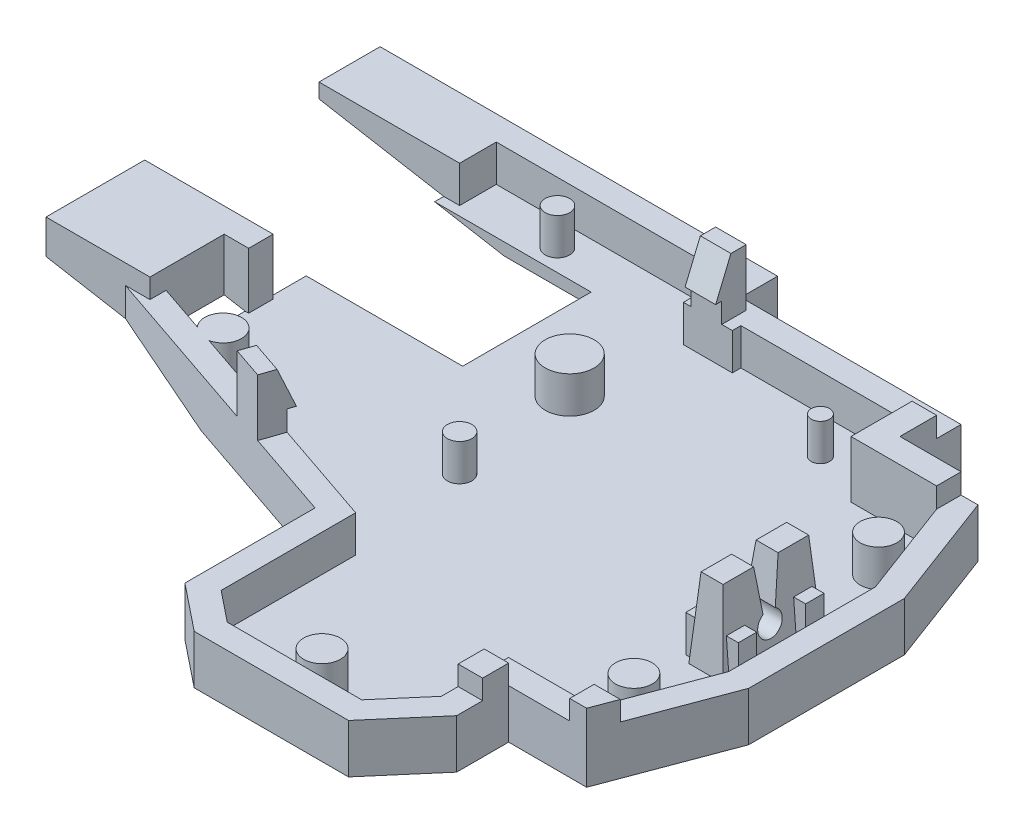
SolidWorks part; units mm, degrees
ref_plane "Front Plane" through (0, 0, 0) normal (0, 0, 1) x (1, 0, 0)
ref_plane "Top Plane" through (0, 0, 0) normal (0, 1, 0) x (1, 0, 0)
ref_plane "Right Plane" through (0, 0, 0) normal (1, 0, 0) x (0, 0, -1)
sketch "Sketch13" plane through (0, 0, 0) normal (0, 1, 0) x (1, 0, 0)
  line L1 (0, 0) -> (50, 0)
  line L2 (0, 0) -> (0, -45)
  line L3 (0, -45) -> (50, -45)
  line L4 (50, 0) -> (50, -45)
  dimension "D1" = 50
extrude "Boss-Extrude4" add sketch "Sketch13" along normal blind 1.6
sketch "Sketch14" plane through (0, 1.6, 0) normal (0, 1, 0) x (1, 0, 0)
  line L1 (50, 0) -> (40, 0)
  line L2 (50, 0) -> (50, -8)
  line L3 (50, -8) -> (40, -8)
  line L4 (40, 0) -> (40, -8)
extrude "Cut-Extrude6" cut sketch "Sketch14" against normal through all
sketch "Sketch15" plane through (0, 1.6, 0) normal (0, 1, 0) x (1, 0, 0)
  line L1 (40, 0) -> (22, 0)
  line L2 (40, 0) -> (40, -3)
  line L3 (40, -3) -> (22, -3)
  line L4 (22, 0) -> (22, -3)
extrude "Cut-Extrude7" cut sketch "Sketch15" against normal through all
sketch "Sketch16" plane through (0, 1.6, 0) normal (0, 1, 0) x (1, 0, 0)
  line L1 (22, -3) -> (26, -3)
  line L2 (22, -3) -> (22, -3.7)
  line L3 (22, -3.7) -> (26, -3.7)
  line L4 (26, -3) -> (26, -3.7)
  dimension "D1" = 0.7
  dimension "D2" = 4
extrude "Cut-Extrude8" cut sketch "Sketch16" against normal through all
sketch "Sketch17" plane through (0, 1.6, 0) normal (0, 1, 0) x (1, 0, 0)
  line L3 (40, -8) -> (50, -8) construction
  line L4 (47, -8) -> (50, -16)
  line L6 (50, -45) -> (50, -8) construction
  line L7 (50, -16) -> (65.8811, -16)
  line L8 (65.8811, -16) -> (65.8811, 17.9573)
  line L9 (65.8811, 17.9573) -> (47, 17.9573)
  line L10 (47, 17.9573) -> (47, -8)
extrude "Cut-Extrude9" cut sketch "Sketch17" against normal through all
sketch "Sketch18" plane through (0, 1.6, 0) normal (0, 1, 0) x (1, 0, 0)
  line L0 (40, -8) -> (40, -36) construction
  line L2 (40, -36) -> (61.1096, -36)
  line L3 (40, -36) -> (40, -58.8405)
  line L4 (40, -58.8405) -> (61.1096, -58.8405)
  line L5 (61.1096, -36) -> (61.1096, -58.8405)
extrude "Cut-Extrude10" cut sketch "Sketch18" against normal through all
sketch "Sketch21" plane through (0, 1.6, 0) normal (0, 1, 0) x (1, 0, 0)
  line L0 (50, -16) -> (27.9365, -16) construction
  line L1 (47, -36) -> (47, -28) construction
  line L2 (50, -36) -> (40, -36) construction
  line L3 (50, -28) -> (47, -36)
  line L4 (50, -36) -> (50, -16) construction
  line L5 (47, -36) -> (47, -49.2976)
  line L6 (47, -49.2976) -> (75.1968, -49.2976)
  line L7 (75.1968, -49.2976) -> (75.1968, -28)
  line L8 (75.1968, -28) -> (50, -28)
extrude "Cut-Extrude11" cut sketch "Sketch21" against normal through all
sketch "Sketch22" plane through (0, 1.6, 0) normal (0, 1, 0) x (1, 0, 0)
  line L0 (0, 0) -> (0, -19.3362) construction
  line L1 (0, 0) -> (0, -45) construction
  line L4 (0, -19.3362) -> (2, -19.3362)
  line L5 (0, -19.3362) -> (0, -22.3362)
  line L6 (0, -22.3362) -> (2, -22.3362)
  line L7 (2, -19.3362) -> (2, -22.3362)
  dimension "D1" = 2
  dimension "D2" = 3
extrude "Cut-Extrude12" cut sketch "Sketch22" against normal through all
sketch "Sketch23" plane through (0, 1.6, 0) normal (0, 1, 0) x (1, 0, 0)
  line L0 (40, -45) -> (23.5, -45) construction
  line L1 (0, -45) -> (40, -45) construction
  line L2 (23.5, -45) -> (23.5, -32)
  line L3 (0, -22.3362) -> (0, -26.3362) construction
  line L4 (0, -22.3362) -> (0, -45) construction
  line L5 (23.5, -32) -> (0, -26.3362)
  line L6 (0, -26.3362) -> (-30.2262, -26.3362)
  line L7 (-30.2262, -26.3362) -> (-30.2262, -63.1883)
  line L8 (-30.2262, -63.1883) -> (23.5, -63.1883)
  line L9 (23.5, -63.1883) -> (23.5, -45)
extrude "Cut-Extrude13" cut sketch "Sketch23" against normal through all
sketch "Sketch24" plane through (0, 1.6, 0) normal (0, 1, 0) x (1, 0, 0)
  line L0 (23.5, -43) -> (7.4911, -43)
  line L1 (23.5, -45) -> (40, -45) construction
  line L2 (7.4911, -43) -> (7.4911, -69.5502)
  line L3 (40, -36) -> (40, -45) construction
  line L4 (37, -45) -> (40, -41.5)
  line L5 (23.5, -45) -> (23.5, -32) construction
  line L6 (26, -45) -> (23.5, -43)
  line L7 (7.4911, -69.5502) -> (44.754, -69.5502)
  line L8 (44.754, -69.5502) -> (44.754, -41.5)
  line L9 (44.754, -41.5) -> (40, -41.5)
  line L10 (37, -45) -> (26, -45)
extrude "Cut-Extrude14" cut sketch "Sketch24" against normal through all
sketch "Sketch25" plane through (0, 1.6, 0) normal (0, 1, 0) x (1, 0, 0)
  line L0 (50, -22) -> (47.6007, -22.0598) construction
  line L1 (50, -28) -> (50, -16) construction
  line L2 (47.6007, -22.0598) -> (47.6007, -18.0598) construction
  line L4 (47.6007, -18.0598) -> (44.8007, -18.0598)
  line L5 (47.6007, -18.0598) -> (47.6007, -26.0598)
  line L6 (47.6007, -26.0598) -> (44.8007, -26.0598)
  line L7 (44.8007, -18.0598) -> (44.8007, -26.0598)
  dimension "D1" = 2.8
  dimension "D2" = 8
extrude "Cut-Extrude15" cut sketch "Sketch25" against normal through all
sketch "Sketch28" plane through (0, 0, 0) normal (0, -1, 0) x (1, 0, 0)
  line L44 (42, 38) -> (42, 42.2398)
  line L45 (42, 42.2398) -> (37.9199, 47)
  line L46 (37.9199, 47) -> (25.2984, 47)
  line L47 (25.2984, 47) -> (21.5, 43.9612)
  line L48 (21.5, 43.9612) -> (21.5, 33.5752)
  line L49 (21.5, 33.5752) -> (-2, 27.9115)
  line L50 (-2, 27.9115) -> (-2, -2)
  line L51 (-2, -2) -> (24, -2)
  line L52 (24, -2) -> (24, 1)
  line L53 (24, 1) -> (42, 1)
  line L54 (42, 1) -> (42, 6)
  line L55 (42, 6) -> (48.386, 6)
  line L56 (48.386, 6) -> (52, 15.6373)
  line L57 (52, 15.6373) -> (52, 28.3627)
  line L58 (52, 28.3627) -> (48.386, 38)
  line L59 (48.386, 38) -> (42, 38)
  line L60 (42, 38) -> (42, 42.2398)
  line L61 (42, 42.2398) -> (37.9199, 47)
  line L62 (37.9199, 47) -> (25.2984, 47)
  line L63 (25.2984, 47) -> (21.5, 43.9612)
  line L64 (21.5, 43.9612) -> (21.5, 33.5752)
  line L65 (21.5, 33.5752) -> (-2, 27.9115)
  line L66 (-2, 27.9115) -> (-2, -2)
  line L67 (-2, -2) -> (24, -2)
  line L68 (24, -2) -> (24, 1)
  line L69 (24, 1) -> (42, 1)
  line L70 (42, 1) -> (42, 6)
  line L71 (42, 6) -> (48.386, 6)
  line L72 (48.386, 6) -> (52, 15.6373)
  line L73 (52, 15.6373) -> (52, 28.3627)
  line L74 (52, 28.3627) -> (48.386, 38)
  line L75 (48.386, 38) -> (42, 38)
  dimension "D1" = 2
extrude "Boss-Extrude6" add sketch "Sketch28" along normal blind 6
sketch "Sketch30" plane through (0, 0, 0) normal (0, 1, 0) x (1, 0, 0)
  line L8 (44.8007, -18.0598) -> (44.8007, -26.0598)
  line L9 (44.8007, -26.0598) -> (47.6007, -26.0598)
  line L10 (47.6007, -26.0598) -> (47.6007, -18.0598)
  line L11 (47.6007, -18.0598) -> (44.8007, -18.0598)
  line L12 (44.8007, -18.0598) -> (44.8007, -26.0598)
  line L13 (44.8007, -26.0598) -> (47.6007, -26.0598)
  line L14 (47.6007, -26.0598) -> (47.6007, -18.0598)
  line L15 (47.6007, -18.0598) -> (44.8007, -18.0598)
  dimension "D1" = 0
extrude "Boss-Extrude7" add sketch "Sketch30" along normal blind 3.5
sketch "Sketch31" plane through (0, 1.6, 0) normal (0, 1, 0) x (1, 0, 0)
  line L44 (37, -45) -> (40, -41.5)
  line L45 (40, -41.5) -> (40, -36)
  line L46 (40, -36) -> (47, -36)
  line L47 (47, -36) -> (50, -28)
  line L48 (50, -28) -> (50, -16)
  line L49 (50, -16) -> (47, -8)
  line L50 (47, -8) -> (40, -8)
  line L51 (40, -8) -> (40, -3)
  line L52 (40, -3) -> (26, -3)
  line L53 (26, -3) -> (26, -3.7)
  line L54 (26, -3.7) -> (22, -3.7)
  line L55 (22, -3.7) -> (22, 0)
  line L56 (22, 0) -> (0, 0)
  line L57 (0, 0) -> (0, -19.3362)
  line L58 (0, -19.3362) -> (2, -19.3362)
  line L59 (2, -19.3362) -> (2, -22.3362)
  line L60 (2, -22.3362) -> (0, -22.3362)
  line L61 (0, -22.3362) -> (0, -26.3362)
  line L62 (0, -26.3362) -> (23.5, -32)
  line L63 (23.5, -32) -> (23.5, -43)
  line L64 (23.5, -43) -> (26, -45)
  line L65 (26, -45) -> (37, -45)
  line L66 (37, -45) -> (40, -41.5)
  line L67 (40, -41.5) -> (40, -36)
  line L68 (40, -36) -> (47, -36)
  line L69 (47, -36) -> (50, -28)
  line L70 (50, -28) -> (50, -16)
  line L71 (50, -16) -> (47, -8)
  line L72 (47, -8) -> (40, -8)
  line L73 (40, -8) -> (40, -3)
  line L74 (40, -3) -> (26, -3)
  line L75 (26, -3) -> (26, -3.7)
  line L76 (26, -3.7) -> (22, -3.7)
  line L77 (22, -3.7) -> (22, 0)
  line L78 (22, 0) -> (0, 0)
  line L79 (0, 0) -> (0, -19.3362)
  line L80 (0, -19.3362) -> (2, -19.3362)
  line L81 (2, -19.3362) -> (2, -22.3362)
  line L82 (2, -22.3362) -> (0, -22.3362)
  line L83 (0, -22.3362) -> (0, -26.3362)
  line L84 (0, -26.3362) -> (23.5, -32)
  line L85 (23.5, -32) -> (23.5, -43)
  line L86 (23.5, -43) -> (26, -45)
  line L87 (26, -45) -> (37, -45)
  dimension "D1" = 0
extrude "Cut-Extrude16" cut sketch "Sketch31" against normal blind 4.6
sketch "Sketch32" plane through (0, 1.6, 0) normal (0, -1, 0) x (1, 0, 0)
  line L8 (47.6007, 18.0598) -> (47.6007, 26.0598)
  line L9 (47.6007, 26.0598) -> (44.8007, 26.0598)
  line L10 (44.8007, 26.0598) -> (44.8007, 18.0598)
  line L11 (44.8007, 18.0598) -> (47.6007, 18.0598)
  line L12 (47.6007, 18.0598) -> (47.6007, 26.0598)
  line L13 (47.6007, 26.0598) -> (44.8007, 26.0598)
  line L14 (44.8007, 26.0598) -> (44.8007, 18.0598)
  line L15 (44.8007, 18.0598) -> (47.6007, 18.0598)
  dimension "D1" = 0
extrude "Boss-Extrude8" add sketch "Sketch32" along normal blind 4.6
sketch "Sketch35" plane through (47.6007, 0, 0) normal (1, 0, 0) x (0, 0, -1)
  line L0 (-22.0598, 3.5) -> (-22.0598, 0) construction
  line L1 (-26.0598, 3.5) -> (-18.0598, 3.5) construction
  line L2 (-22.0598, 3.5) -> (-21.0598, 3.5) construction
  line L3 (-22.0598, 3.5) -> (-23.0598, 3.5) construction
  line L4 (-22.0598, 0) -> (-21.5598, 0)
  line L5 (-21.5598, 0) -> (-21.0598, 3.5)
  line L6 (-22.0598, 0) -> (-22.5598, 0)
  line L7 (-22.5598, 0) -> (-23.0598, 3.5)
  line L8 (-23.0598, 3.5) -> (-23.2577, 4.8851)
  line L9 (-21.0598, 3.5) -> (-21.2977, 5.1651)
  line L10 (-21.2977, 5.1651) -> (-23.2577, 4.8851)
extrude "Cut-Extrude18" cut sketch "Sketch35" against normal blind 4.6
sketch "Sketch37" plane through (47.6007, 0, 0) normal (1, 0, 0) x (0, 0, -1)
  line L0 (-22.0598, 0) -> (-22.0598, -3.4808) construction
  line L1 (-22.5598, 0) -> (-21.5598, 0) construction
  line L2 (-21.5598, 0) -> (-22.0598, -0.866) construction
  circle A0 centre (-22.0598, -0.866) radius 1
extrude "Cut-Extrude19" cut sketch "Sketch37" against normal blind 4.6
sketch "Sketch39" plane through (44.8007, 0, 0) normal (-1, 0, 0) x (0, 0, 1)
  line L0 (26.0598, 3.5) -> (25.5598, 3.5) construction
  line L1 (23.0598, 3.5) -> (26.0598, 3.5) construction
  line L2 (25.5598, 3.5) -> (26.0598, -3)
  line L3 (26.0598, -3) -> (27.9064, -2.858)
  line L4 (27.9064, -2.858) -> (27.4064, 3.642)
  line L5 (27.4064, 3.642) -> (25.5598, 3.5)
  line L6 (18.0598, 3.5) -> (18.5598, 3.5) construction
  line L7 (18.0598, 3.5) -> (21.0598, 3.5) construction
  line L8 (18.5598, 3.5) -> (18.0598, -3)
  line L9 (18.0598, -3) -> (15.9573, -2.8383)
  line L10 (15.9573, -2.8383) -> (16.4557, 3.642)
  line L11 (16.4557, 3.642) -> (18.5598, 3.5)
extrude "Cut-Extrude20" cut sketch "Sketch39" against normal blind 4.6
sketch "Sketch41" plane through (0, 0, 0) normal (0, 0, 1) x (1, 0, 0)
  line L0 (44.8007, 3.5) -> (45.3007, 3.5) construction
  line L1 (44.8007, 3.5) -> (47.6007, 3.5) construction
  line L2 (47.6007, 3.5) -> (47.1007, 3.5) construction
  line L3 (45.3007, 3.5) -> (44.8007, -3)
  line L4 (44.8007, -3) -> (43.415, -2.8934)
  line L5 (43.415, -2.8934) -> (43.9406, 3.9398)
  line L6 (43.9406, 3.9398) -> (45.3007, 3.5)
  line L7 (47.1007, 3.5) -> (47.6007, -3)
  line L8 (47.6007, -3) -> (49.659, -2.8417)
  line L9 (49.659, -2.8417) -> (49.1373, 3.9398)
  line L10 (49.1373, 3.9398) -> (47.1007, 3.5)
extrude "Cut-Extrude21" cut sketch "Sketch41" along normal up to vertex
sketch "Sketch43" plane through (0, 0, 0) normal (0, 1, 0) x (1, 0, 0)
  line L0 (47, -8) -> (50, -16)
  line L1 (50, -16) -> (51.1704, -13.4251)
  line L2 (49.4404, -8.8117) -> (52, -15.6373) construction
  line L3 (46.2007, -6) -> (51.8278, -6) construction
  line L4 (45.0315, -6) -> (47.37, -6) construction
  line L5 (50.6159, -11.9464) -> (47.8466, -4.5615) construction
  line L6 (51.1704, -13.4251) -> (48.386, -6)
  line L7 (48.386, -6) -> (42.8188, -6)
  line L8 (42, -6) -> (43.6375, -6) construction
  line L9 (42.8188, -6) -> (42.8188, -8)
  line L10 (40, -8) -> (43.6375, -8) construction
  line L11 (42.8188, -8) -> (47, -8)
extrude "Boss-Extrude9" add sketch "Sketch43" against normal blind 4.6
sketch "Sketch44" plane through (0, -3, 0) normal (0, 1, 0) x (1, 0, 0)
  line L0 (47.6007, -18.0598) -> (47.6007, -18.5598) construction
  line L1 (47.6007, -18.0598) -> (47.6007, -26.0598) construction
  line L2 (47.6007, -18.5598) -> (48.3507, -18.5598) construction
  line L3 (44.8007, -18.5598) -> (44.0507, -18.5598) construction
  line L4 (44.8007, -26.0598) -> (44.8007, -18.0598) construction
  line L5 (47.6007, -26.0598) -> (47.6007, -25.5598) construction
  line L6 (48.3507, -25.5598) -> (44.0507, -25.5598) construction
  line L7 (48.3507, -18.5598) -> (48.3507, -20.0598)
  line L8 (48.3507, -25.5598) -> (48.3507, -24.0598)
  line L9 (48.3507, -24.0598) -> (44.0507, -24.0598)
  line L10 (44.0507, -24.0598) -> (44.0507, -25.5598)
  line L11 (44.0507, -25.5598) -> (48.3507, -25.5598)
  line L12 (48.3507, -20.0598) -> (44.0507, -20.0598)
  line L13 (44.0507, -20.0598) -> (44.0507, -18.5598)
  line L14 (44.0507, -18.5598) -> (48.3507, -18.5598)
extrude "Boss-Extrude11" add sketch "Sketch44" along normal blind 3
sketch "Sketch45" plane through (0, -3, 0) normal (0, 1, 0) x (1, 0, 0)
  line L0 (50, -22) -> (44, -22) construction
  line L1 (50, -28) -> (50, -16) construction
  line L2 (44, -22) -> (44, -32) construction
  line L3 (44, -32) -> (46.25, -32) construction
  line L4 (44, -22) -> (44, -12) construction
  line L5 (22, -3.7) -> (22, -22) construction
  line L6 (22, -22) -> (22, -21) construction
  line L7 (40, -36) -> (23.5, -36) construction
  line L8 (23.5, -32) -> (23.5, -43) construction
  line L9 (31.75, -45) -> (31.75, -43) construction
  line L10 (26, -45) -> (37, -45) construction
  line L11 (40, -3) -> (40, -6) construction
  line L12 (40, -8) -> (40, -3) construction
  line L13 (40, -6) -> (35.5, -6) construction
  line L14 (22, 0) -> (22, -2) construction
  line L15 (22, 0) -> (0, 0) construction
  line L16 (22, -3.7) -> (22, 0) construction
  line L17 (22, -2) -> (10, -2) construction
  line L18 (0, -24.3362) -> (5, -24.3362) construction
  line L19 (0, -22.3362) -> (0, -26.3362) construction
  circle A0 centre (46.25, -12) radius 1.5
  circle A1 centre (46.25, -32) radius 1.5
  circle A2 centre (22, -22) radius 1
  circle A3 centre (21, -12) radius 1.9996
  circle A4 centre (31.75, -43) radius 1.5033
  circle A5 centre (35.5, -6) radius 0.75
  circle A6 centre (10, -2) radius 1
  circle A7 centre (5, -24.3362) radius 1.5
extrude "Boss-Extrude12" add sketch "Sketch45" along normal blind 3
sketch "Sketch46" plane through (0, 0, 0) normal (0, 1, 0) x (1, 0, 0)
  line L0 (14.1373, -29.7435) -> (16.5677, -30.3292)
  line L1 (16.5677, -30.3292) -> (16.0991, -32.2736)
  line L2 (21.5, -33.5752) -> (-2, -27.9115) construction
  line L3 (16.0991, -32.2736) -> (13.6687, -31.6878)
  line L4 (13.6687, -31.6878) -> (14.1373, -29.7435)
  line L5 (24, -3.7) -> (25.1336, -3.7) construction
  line L6 (22, -3.7) -> (26, -3.7) construction
  line L7 (25.1336, -3.7) -> (22.6336, -3.7)
  line L8 (22.6336, -3.7) -> (22.6336, -1.7)
  line L9 (22.6336, -1.7) -> (25.1336, -1.7)
  line L10 (25.1336, -1.7) -> (25.1336, -3.7)
  line L11 (2, -20.8362) -> (2, -19.9327) construction
  line L12 (2, -22.3362) -> (2, -19.3362) construction
  line L13 (2, -19.9327) -> (2, -21.9327)
  line L14 (2, -21.9327) -> (0, -21.9327)
  line L15 (0, -21.9327) -> (0, -19.9327)
  line L16 (0, -19.9327) -> (2, -19.9327)
  line L17 (23.5, -32) -> (0, -26.3362) construction
  line L18 (16.5677, -30.3292) -> (14.1373, -29.7435) construction
  line L19 (47, -36) -> (48.8727, -36.7022)
  line L20 (52, -28.3627) -> (48.386, -38) construction
  line L21 (48.8727, -36.7022) -> (49.7505, -34.3614)
  line L22 (49.7505, -34.3614) -> (47.8778, -33.6592)
  line L23 (50, -28) -> (47, -36) construction
  line L24 (47.8778, -33.6592) -> (47, -36)
  line L25 (40, -3) -> (40, -8)
  line L26 (26, -3) -> (40, -3) construction
  line L27 (40, -3) -> (40, -8) construction
  line L28 (40, -8) -> (47, -8)
  line L29 (47, -8) -> (47, -6)
  line L30 (42, -6) -> (48.386, -6) construction
  line L31 (47, -6) -> (42, -6)
  line L32 (42, -6) -> (42, -3)
  line L33 (42, -1) -> (42, -6) construction
  line L34 (42, -3) -> (40, -3)
extrude "Boss-Extrude13" add sketch "Sketch46" along normal blind 1.65
sketch "Sketch47" plane through (0, 0, 0) normal (0, 1, 0) x (1, 0, 0)
  line L1 (0, 0) -> (3, 0)
  line L2 (0, 0) -> (0, -3)
  line L3 (0, -3) -> (3, -3)
  line L4 (3, 0) -> (3, -3)
extrude "Boss-Extrude14" add sketch "Sketch47" against normal up to surface (3 mm away) up to face at (10, -3, 3)
sketch "Sketch48" plane through (0, 0, 0) normal (0, 1, 0) x (1, 0, 0)
  line L0 (-2, -27.9115) -> (-2, 2) construction
  line L1 (0, -19.3362) -> (-2, -19.3362)
  line L2 (0, -19.3362) -> (0, -3)
  line L3 (0, -3) -> (-2, -3)
  line L4 (-2, -19.3362) -> (-2, -3)
extrude "Cut-Extrude22" cut sketch "Sketch48" against normal up to surface (3 mm away) up to face at (23.75, -3, 19.4826)
sketch "Sketch49" plane through (-2, 0, 0) normal (-1, 0, 0) x (0, 0, 1)
  line L1 (-2, -6) -> (19.3362, -6)
  line L2 (-2, -6) -> (-2, -3)
  line L3 (-2, -3) -> (19.3362, -3)
  line L4 (19.3362, -6) -> (19.3362, -3)
extrude "Boss-Extrude15" add sketch "Sketch49" along normal blind 13
sketch "Sketch50" plane through (0, -6, 0) normal (0, -1, 0) x (1, 0, 0)
  line L0 (52, 22) -> (52, -11.4177) construction
  line L1 (52, 15.6373) -> (52, 28.3627) construction
  line L2 (24, -2) -> (52, -2) construction
  line L3 (52, 22) -> (52, 58.8348) construction
  line L4 (34.4271, 47) -> (52, 47) construction
  line L5 (37.9199, 47) -> (25.2984, 47) construction
  line L7 (-15, -2) -> (52, -2)
  line L8 (-15, -2) -> (-15, 47)
  line L9 (-15, 47) -> (52, 47)
  line L10 (52, -2) -> (52, 47)
extrude "Boss-Extrude16" add sketch "Sketch50" against normal up to surface (3 mm away) up to face at (19.6296, -3, 17.9784)
sketch "Sketch51" plane through (0, -3, 0) normal (0, 1, 0) x (1, 0, 0)
  line L0 (47.6007, -26.0598) -> (47.6007, -47) construction
  line L1 (52, -47) -> (37.9199, -47) construction
  line L3 (47, -36) -> (52, -36)
  line L4 (47, -36) -> (47, -47)
  line L5 (47, -47) -> (52, -47)
  line L6 (52, -36) -> (52, -47)
extrude "Boss-Extrude17" add sketch "Sketch51" along normal blind 15.6
sketch "Sketch52" plane through (0, 1.65, 0) normal (0, 1, 0) x (1, 0, 0)
  line L8 (47.8778, -33.6592) -> (47, -36)
  line L9 (47, -36) -> (49.136, -36)
  line L10 (49.136, -36) -> (49.7505, -34.3614)
  line L11 (49.7505, -34.3614) -> (47.8778, -33.6592)
  line L12 (47.8778, -33.6592) -> (47, -36)
  line L13 (47, -36) -> (49.136, -36)
  line L14 (49.136, -36) -> (49.7505, -34.3614)
  line L15 (49.7505, -34.3614) -> (47.8778, -33.6592)
  dimension "D1" = 0
extrude "Cut-Extrude23" cut sketch "Sketch52" against normal up to surface (1.65 mm away) up to face at (49.3349, 0, 19.5578)
sketch "Sketch53" plane through (0, 0, 0) normal (0, 1, 0) x (1, 0, 0)
  line L0 (40, -36) -> (40, -41.5) construction
  line L1 (40, -37.9906) -> (42, -37.9906)
  line L2 (40, -37.9906) -> (40, -40.1199)
  line L3 (40, -40.1199) -> (42, -40.1199)
  line L4 (42, -37.9906) -> (42, -40.1199)
  line L5 (42, -38) -> (42, -42.2398) construction
extrude "Boss-Extrude18" add sketch "Sketch53" along normal blind 1.6
sketch "Sketch55" plane through (0, 1.65, 0) normal (0, 1, 0) x (1, 0, 0)
  line L1 (22.6336, -1.7) -> (25.1336, -1.7)
  line L2 (22.6336, -1.7) -> (22.6336, -4.2)
  line L3 (22.6336, -4.2) -> (25.1336, -4.2)
  line L4 (25.1336, -1.7) -> (25.1336, -4.2)
extrude "Boss-Extrude20" add sketch "Sketch55" along normal blind 3
sketch "Sketch56" plane through (25.1336, 0, 0) normal (1, 0, 0) x (0, 0, -1)
  line L0 (-4.2, 1.65) -> (-2.95, 4.65)
  line L1 (-4.2, 4.65) -> (-1.7, 4.65) construction
  line L2 (-2.95, 4.65) -> (-2.95, 7.6873)
  line L3 (-2.95, 7.6873) -> (-6.5972, 7.6873)
  line L4 (-6.5972, 7.6873) -> (-6.5972, 1.6413)
  line L5 (-6.5972, 1.6413) -> (-4.2, 1.65)
extrude "Cut-Extrude24" cut sketch "Sketch56" against normal blind 3
sketch "Sketch58" plane through (0, -3, 0) normal (0, 1, 0) x (1, 0, 0)
  line L0 (3, 0) -> (-15, 0) construction
  line L1 (-15, -47) -> (-15, 2) construction
  line L2 (0, -26.3362) -> (7.3396, -26.3362) construction
  line L3 (-15, -19.3362) -> (-15, -16.4918) construction
  line L4 (3, 0) -> (3, -3.75) construction
  line L5 (3, -3.75) -> (-5.5, -3.75) construction
  line L6 (-5.5, -3.75) -> (14.5, -3.75)
  line L7 (-5.5, -3.75) -> (-5.5, -14.25)
  line L8 (-5.5, -14.25) -> (14.5, -14.25)
  line L9 (14.5, -3.75) -> (14.5, -14.25)
  line L10 (7.3396, 0) -> (7.3396, -26.3362) construction
  line L11 (22, 0) -> (3, 0) construction
  line L12 (26, -45) -> (6.087, -45) construction
  line L13 (6.087, 0) -> (6.087, -45) construction
  line L14 (0, 0) -> (0, -25) construction
  line L15 (0, -22.3362) -> (0, -26.3362) construction
  line L16 (0, -14.25) -> (0, -17.2489) construction
  line L17 (2, -20.8362) -> (2, -17.2489) construction
  line L18 (2, -19.3362) -> (2, -22.3362) construction
  line L19 (0, -17.2489) -> (2, -17.2489)
  line L20 (2, -17.2489) -> (2, -19.2489)
  line L21 (2, -19.2489) -> (0, -19.2489)
  line L22 (0, -19.2489) -> (0, -17.2489)
extrude "Cut-Extrude29" cut sketch "Sketch58" against normal blind 1
sketch "Sketch60" plane through (0, -3, 0) normal (0, 1, 0) x (1, 0, 0)
  line L0 (27.9182, -45) -> (13.2629, -45) construction
  line L1 (26, -45) -> (37, -45) construction
  line L2 (23.5, -32) -> (23.5, -45) construction
  line L3 (0, 0) -> (0, -24) construction
  line L4 (0, -22.3362) -> (0, -26.3362) construction
  line L5 (0, -24) -> (23.5, -32)
  line L6 (23.5, -32) -> (0, -26.3362)
  line L7 (0, -26.3362) -> (23.5, -32) construction
  line L8 (0, -26.3362) -> (0, -24)
extrude "Boss-Extrude21" add sketch "Sketch60" along normal up to surface (3 mm away) up to face at (21.502, 0, 1.8353)
sketch "Sketch61" plane through (-5.9989, 0, 24.8904) normal (0.2343, 0, -0.9722) x (-0.9722, 0, -0.2343)
  line L8 (-23.2128, 1.65) -> (-23.2128, 0)
  line L9 (-23.2128, 0) -> (-20.7128, 0)
  line L10 (-20.7128, 0) -> (-20.7128, 1.65)
  line L11 (-20.7128, 1.65) -> (-23.2128, 1.65)
  line L12 (-23.2128, 1.65) -> (-23.2128, 0)
  line L13 (-23.2128, 0) -> (-20.7128, 0)
  line L14 (-20.7128, 0) -> (-20.7128, 1.65)
  line L15 (-20.7128, 1.65) -> (-23.2128, 1.65)
  dimension "D1" = 0
extrude "Boss-Extrude22" add sketch "Sketch61" along normal up to surface (0.8848 mm away)
sketch "Sketch62" plane through (0, 0, 0) normal (0, 1, 0) x (1, 0, 0)
  line L0 (0, -24) -> (0, -26) construction
  line L1 (1.9318, -24.6576) -> (-9.2599, -20.8477) construction
  line L2 (3.8635, -25.3152) -> (0, -24) construction
  line L3 (-9.2599, -20.8477) -> (-9.2599, -22.8477) construction
  line L4 (0, -26) -> (-0.5452, -28.2621)
  line L5 (13.6687, -31.6878) -> (-2, -27.9115) construction
  line L6 (-0.5452, -28.2621) -> (-9.9311, -26)
  line L7 (-9.9311, -26) -> (-9.2599, -22.8477)
  line L8 (-9.2599, -22.8477) -> (0, -26)
extrude "Cut-Extrude30" cut sketch "Sketch62" against normal up to surface (3 mm away) up to face at (35.5, -3, 6.75)
sketch "Sketch63" plane through (-6.4675, 0, 26.8348) normal (-0.2343, 0, 0.9722) x (0.9722, 0, 0.2343)
  line L16 (20.7128, 0) -> (6.0919, 0)
  line L17 (6.0919, 0) -> (6.0919, -3)
  line L18 (6.0919, -3) -> (28.7683, -3)
  line L19 (28.7683, -3) -> (28.7683, 0)
  line L20 (28.7683, 0) -> (23.2128, 0)
  line L21 (23.2128, 0) -> (23.2128, 1.65)
  line L22 (23.2128, 1.65) -> (20.7128, 1.65)
  line L23 (20.7128, 1.65) -> (20.7128, 0)
  line L24 (20.7128, 0) -> (6.0919, 0)
  line L25 (6.0919, 0) -> (6.0919, -3)
  line L26 (6.0919, -3) -> (28.7683, -3)
  line L27 (28.7683, -3) -> (28.7683, 0)
  line L28 (28.7683, 0) -> (23.2128, 0)
  line L29 (23.2128, 0) -> (23.2128, 1.65)
  line L30 (23.2128, 1.65) -> (20.7128, 1.65)
  line L31 (20.7128, 1.65) -> (20.7128, 0)
  dimension "D1" = 0
extrude "Cut-Extrude31" cut sketch "Sketch63" against normal up to surface (0.7539 mm away)
sketch "Sketch64" plane through (0, 1.65, 0) normal (0, 1, 0) x (1, 0, 0)
  line L0 (0, -21.9327) -> (0, -22.9624) construction
  line L2 (0, -22.9624) -> (2.5515, -22.9624)
  line L3 (0, -22.9624) -> (0, -18.6516)
  line L4 (0, -18.6516) -> (2.5515, -18.6516)
  line L5 (2.5515, -22.9624) -> (2.5515, -18.6516)
extrude "Cut-Extrude32" cut sketch "Sketch64" against normal up to surface (4.65 mm away) up to face at (18.4683, -3, 21.8358)
sketch "Sketch65" plane through (0, -4, 0) normal (0, 1, 0) x (1, 0, 0)
  line L8 (0, -17.2489) -> (0, -19.2489)
  line L9 (0, -19.2489) -> (2, -19.2489)
  line L10 (2, -19.2489) -> (2, -17.2489)
  line L11 (2, -17.2489) -> (0, -17.2489)
  line L12 (0, -17.2489) -> (0, -19.2489)
  line L13 (0, -19.2489) -> (2, -19.2489)
  line L14 (2, -19.2489) -> (2, -17.2489)
  line L15 (2, -17.2489) -> (0, -17.2489)
  dimension "D1" = 0
extrude "Boss-Extrude23" add sketch "Sketch65" along normal up to surface (4 mm away) up to face at (21.502, 0, 1.8353)
sketch "Sketch66" plane through (0, 0, 0) normal (0, 1, 0) x (1, 0, 0)
  line L1 (0, -19.2489) -> (2, -19.2489)
  line L2 (0, -19.2489) -> (0, -17.2489)
  line L3 (0, -17.2489) -> (2, -17.2489)
  line L4 (2, -19.2489) -> (2, -17.2489)
extrude "Boss-Extrude24" add sketch "Sketch66" along normal blind 1.6
sketch "Sketch67" plane through (0, 1.6, 0) normal (0, 1, 0) x (1, 0, 0)
  line L0 (0, -19.2489) -> (2.5, -19.2489)
  line L1 (0, -19.2489) -> (0, -17.2489)
  line L2 (0, -17.2489) -> (2.5, -17.2489)
  line L3 (2.5, -17.2489) -> (2.5, -19.2489)
extrude "Boss-Extrude25" add sketch "Sketch67" along normal blind 3
sketch "Sketch68" plane through (0, 0, 17.2489) normal (0, 0, -1) x (-1, 0, 0)
  line L0 (-2.5, 1.6) -> (-1.25, 4.6)
  line L1 (-2.5, 4.6) -> (0, 4.6) construction
  line L2 (-1.25, 4.6) -> (-1.25, 6.7749)
  line L3 (-1.25, 6.7749) -> (-4.4975, 6.7749)
  line L4 (-4.4975, 6.7749) -> (-4.4975, 1.5671)
  line L5 (-4.4975, 1.5671) -> (-2.5, 1.6)
extrude "Cut-Extrude33" cut sketch "Sketch68" against normal blind 3
sketch "Sketch69" plane through (0, 1.65, 0) normal (0, 1, 0) x (1, 0, 0)
  line L0 (14.3446, -28.8833) -> (16.7212, -29.6923) construction
  line L1 (16.7212, -29.6923) -> (18.8289, -30.4098) construction
  line L2 (16.2758, -31.5407) -> (16.8859, -29.7484) construction
  line L3 (16.2758, -31.5407) -> (16.7212, -29.6923) construction
  line L4 (16.2758, -31.5407) -> (13.8992, -30.7316) construction
  line L5 (14.3446, -28.8833) -> (16.8859, -29.7484)
  line L6 (16.8859, -29.7484) -> (16.2758, -31.5407)
  line L7 (16.2758, -31.5407) -> (12.9279, -30.401) construction
  line L8 (14.3446, -28.8833) -> (13.7345, -30.6756)
  line L9 (13.7345, -30.6756) -> (16.2758, -31.5407)
extrude "Boss-Extrude26" add sketch "Sketch69" against normal up to surface (1.65 mm away) up to face at (21.502, 0, 1.8353)
sketch "Sketch70" plane through (0, 0, 19.2489) normal (0, 0, 1) x (1, 0, 0)
  line L0 (2.5, 1.6) -> (1.25, 4.6) construction
  line L1 (2.5, 1.6) -> (-2.555, 1.6)
  line L2 (2.5, 1.6) -> (2.5, 7.1604)
  line L3 (2.5, 7.1604) -> (-2.555, 7.1604)
  line L4 (-2.555, 1.6) -> (-2.555, 7.1604)
extrude "Cut-Extrude34" cut sketch "Sketch70" against normal blind 3
sketch "Sketch71" plane through (0, 1.65, 0) normal (0, 1, 0) x (1, 0, 0)
  line L0 (16.2758, -31.5407) -> (17.0814, -29.1741)
  line L1 (16.2758, -31.5407) -> (13.7345, -30.6756)
  line L2 (18.2187, -25.945) -> (17.0814, -29.1741) construction
  line L3 (18.2187, -25.945) -> (16.2758, -31.5407) construction
  line L4 (17.0814, -29.1741) -> (11.4228, -27.2093) construction
  line L5 (13.7345, -30.6756) -> (14.5598, -28.2985)
  line L6 (14.5598, -28.2985) -> (17.0814, -29.1741)
extrude "Boss-Extrude27" add sketch "Sketch71" along normal blind 3
sketch "Sketch72" plane through (24.2076, 0, 8.2409) normal (0.9466, 0, 0.3223) x (0.3223, 0, -0.9466)
  line L0 (-22.1129, 1.65) -> (-23.3629, 4.65)
  line L1 (-24.6129, 4.65) -> (-22.1129, 4.65) construction
  line L2 (-23.3629, 4.65) -> (-23.3629, 7.6948)
  line L3 (-23.3629, 7.6948) -> (-20.7348, 7.6948)
  line L4 (-20.7348, 7.6948) -> (-20.7348, 1.65)
  line L5 (-20.7348, 1.65) -> (-22.1129, 1.65)
extrude "Cut-Extrude35" cut sketch "Sketch72" against normal blind 3
sketch "Sketch73" plane through (21.762, 0, 7.5561) normal (-0.9447, 0, -0.328) x (-0.328, 0, 0.9447)
  line L10 (24.4734, 4.65) -> (23.2234, 4.65)
  line L11 (23.2234, 4.65) -> (21.9734, 1.65)
  line L12 (21.9734, 1.65) -> (22.5801, 1.65)
  line L13 (22.5801, 1.65) -> (24.4734, 1.65)
  line L14 (24.4734, 1.65) -> (24.4734, 4.65)
  line L15 (24.4734, 4.65) -> (23.2234, 4.65)
  line L16 (23.2234, 4.65) -> (21.9734, 1.65)
  line L17 (21.9734, 1.65) -> (22.5801, 1.65)
  line L18 (22.5801, 1.65) -> (24.4734, 1.65)
  line L19 (24.4734, 1.65) -> (24.4734, 4.65)
  dimension "D1" = 0
extrude "Boss-Extrude28" add sketch "Sketch73" along normal up to surface (0.0115 mm away)
sketch "Sketch74" plane through (0, -4, 0) normal (0, 1, 0) x (1, 0, 0)
  line L0 (-5.5, -9) -> (14.5, -9) construction
  line L1 (-5.5, -3.75) -> (-5.5, -14.25) construction
  line L2 (14.5, -14.25) -> (14.5, -3.75) construction
  line L3 (-0.25, -6.1692) -> (-0.25, -11.6692) construction
  line L4 (4.5, -6.1692) -> (4.5, -11.6692) construction
  line L5 (-0.25, -6.1692) -> (9.25, -6.1692) construction
  line L6 (9.25, -6.1692) -> (9.25, -11.6692) construction
  line L7 (2.5808, -9) -> (-0.25, -6.1692) construction
  line L8 (6.4192, -6.1692) -> (2.5808, -6.1692)
  line L9 (9.25, -6.1692) -> (6.4192, -9) construction
  line L10 (6.4192, -11.8308) -> (2.5808, -11.8308)
  arc A0 (2.5808, -6.1692) -> (2.5808, -11.8308) centre (2.5808, -9) ccw
  arc A1 (6.4192, -6.1692) -> (6.4192, -11.8308) centre (6.4192, -9) cw
extrude "Cut-Extrude36" cut sketch "Sketch74" against normal blind 3
fillet "Fillet8" radius 1 4 edges at (-0.25, -6, 9) (4.5, -6, 6.1692) (9.25, -6, 9) (4.5, -6, 11.8308)
sketch "Sketch76" plane through (0, -3, 0) normal (0, 1, 0) x (1, 0, 0)
  line L0 (47, -47) -> (-8, -47) construction
  line L1 (25.2984, -47) -> (-15, -47) construction
  line L2 (-15, -47) -> (-15, -32.5)
  line L3 (-15, -47) -> (-15, 2) construction
  line L4 (-15, -32.5) -> (-8, -32.5)
  line L5 (-8, -32.5) -> (-8, -47)
  line L6 (-8, -47) -> (-15, -47)
extrude "Boss-Extrude29" add sketch "Sketch76" along normal blind 14.5
sketch "Sketch79" plane through (21.6663, 0, 7.3758) normal (-0.9466, 0, -0.3223) x (-0.3223, 0, 0.9466)
  line L12 (22.7196, 0) -> (24.6129, 0)
  line L13 (24.6129, 0) -> (24.6129, 4.65)
  line L14 (24.6129, 4.65) -> (23.3629, 4.65)
  line L15 (23.3629, 4.65) -> (22.1128, 1.65)
  line L16 (22.1128, 1.65) -> (22.7196, 1.65)
  line L17 (22.7196, 1.65) -> (22.7196, 0)
  line L18 (22.7196, 0) -> (24.6129, 0)
  line L19 (24.6129, 0) -> (24.6129, 4.65)
  line L20 (24.6129, 4.65) -> (23.3629, 4.65)
  line L21 (23.3629, 4.65) -> (22.1128, 1.65)
  line L22 (22.1128, 1.65) -> (22.7196, 1.65)
  line L23 (22.7196, 1.65) -> (22.7196, 0)
  dimension "D1" = 0
extrude "Boss-Extrude30" add sketch "Sketch79" along normal blind 2
sketch "Sketch80" plane through (24.2076, 0, 8.2409) normal (0.9466, 0, 0.3223) x (0.3223, 0, -0.9466)
  line L12 (-22.1129, 1.65) -> (-23.3629, 4.65)
  line L13 (-23.3629, 4.65) -> (-24.6129, 4.65)
  line L14 (-24.6129, 4.65) -> (-24.6129, 0)
  line L15 (-24.6129, 0) -> (-22.7196, 0)
  line L16 (-22.7196, 0) -> (-22.7196, 1.65)
  line L17 (-22.7196, 1.65) -> (-22.1129, 1.65)
  line L18 (-22.1129, 1.65) -> (-23.3629, 4.65)
  line L19 (-23.3629, 4.65) -> (-24.6129, 4.65)
  line L20 (-24.6129, 4.65) -> (-24.6129, 0)
  line L21 (-24.6129, 0) -> (-22.7196, 0)
  line L22 (-22.7196, 0) -> (-22.7196, 1.65)
  line L23 (-22.7196, 1.65) -> (-22.1129, 1.65)
  dimension "D1" = 0
extrude "Cut-Extrude37" cut sketch "Sketch80" against normal blind 2
sketch "Sketch83" plane through (19.773, 0, 6.7312) normal (-0.9466, 0, -0.3223) x (-0.3223, 0, 0.9466)
  line L12 (22.7196, 1.65) -> (22.7196, 0)
  line L13 (22.7196, 0) -> (24.6129, 0)
  line L14 (24.6129, 0) -> (24.6129, 4.65)
  line L15 (24.6129, 4.65) -> (23.3629, 4.65)
  line L16 (23.3629, 4.65) -> (22.1128, 1.65)
  line L17 (22.1128, 1.65) -> (22.7196, 1.65)
  line L18 (22.7196, 1.65) -> (22.7196, 0)
  line L19 (22.7196, 0) -> (24.6129, 0)
  line L20 (24.6129, 0) -> (24.6129, 4.65)
  line L21 (24.6129, 4.65) -> (23.3629, 4.65)
  line L22 (23.3629, 4.65) -> (22.1128, 1.65)
  line L23 (22.1128, 1.65) -> (22.7196, 1.65)
  dimension "D1" = 0
extrude "Boss-Extrude31" add sketch "Sketch83" against normal up to surface (2.6845 mm away) up to face at (14.7873, 2.1, 29.7071)
sketch "Sketch85" plane through (0, -3, 0) normal (0, 1, 0) x (1, 0, 0)
  line L1 (-8, -32.5) -> (22.5662, -32.5)
  line L2 (-8, -32.5) -> (-8, -34.2252)
  line L3 (-8, -34.2252) -> (22.5662, -34.2252)
  line L4 (22.5662, -32.5) -> (22.5662, -34.2252)
extrude "Boss-Extrude33" add sketch "Sketch85" along normal up to surface (3 mm away) up to face at (21.502, 0, 1.8353)
sketch "Sketch86" plane through (0, -3, 0) normal (0, 1, 0) x (1, 0, 0)
  line L10 (21.5, -43.9612) -> (21.5, -34.2252)
  line L11 (21.5, -34.2252) -> (-8, -34.2252)
  line L12 (-8, -34.2252) -> (-8, -47)
  line L13 (-8, -47) -> (25.2984, -47)
  line L14 (25.2984, -47) -> (21.5, -43.9612)
  line L15 (21.5, -43.9612) -> (21.5, -34.2252)
  line L16 (21.5, -34.2252) -> (-8, -34.2252)
  line L17 (-8, -34.2252) -> (-8, -47)
  line L18 (-8, -47) -> (25.2984, -47)
  line L19 (25.2984, -47) -> (21.5, -43.9612)
  dimension "D1" = 0
extrude "Boss-Extrude34" add sketch "Sketch86" along normal up to surface (3 mm away) up to face at (21.502, 0, 1.8353)
sketch "Sketch87" plane through (0, -3, 0) normal (0, 1, 0) x (1, 0, 0)
  line L10 (37.9199, -47) -> (47, -47)
  line L11 (47, -47) -> (47, -38)
  line L12 (47, -38) -> (42, -38)
  line L13 (42, -38) -> (42, -42.2398)
  line L14 (42, -42.2398) -> (37.9199, -47)
  line L15 (37.9199, -47) -> (47, -47)
  line L16 (47, -47) -> (47, -38)
  line L17 (47, -38) -> (42, -38)
  line L18 (42, -38) -> (42, -42.2398)
  line L19 (42, -42.2398) -> (37.9199, -47)
  dimension "D1" = 0
extrude "Boss-Extrude35" add sketch "Sketch87" along normal up to surface (3 mm away) up to face at (21.502, 0, 1.8353)
sketch "Sketch88" plane through (0, 0, 0) normal (0, 1, 0) x (1, 0, 0)
  line L1 (-8, -47) -> (19.0938, -47)
  line L2 (-8, -47) -> (-8, -32.5)
  line L3 (-8, -32.5) -> (19.0938, -32.5)
  line L4 (19.0938, -47) -> (19.0938, -32.5)
extrude "Boss-Extrude36" add sketch "Sketch88" along normal blind 1.6
sketch "Sketch90" plane through (0, 11.5, 0) normal (0, 1, 0) x (1, 0, 0)
  line L8 (-15, -47) -> (-8, -47)
  line L9 (-8, -47) -> (-8, -32.5)
  line L10 (-8, -32.5) -> (-15, -32.5)
  line L11 (-15, -32.5) -> (-15, -47)
  line L12 (-15, -47) -> (-8, -47)
  line L13 (-8, -47) -> (-8, -32.5)
  line L14 (-8, -32.5) -> (-15, -32.5)
  line L15 (-15, -32.5) -> (-15, -47)
  dimension "D1" = 0
extrude "Boss-Extrude37" add sketch "Sketch90" along normal blind 1.6
sketch "Sketch93" plane through (0, 12.6, 0) normal (0, 1, 0) x (1, 0, 0)
  line L1 (47, -47) -> (52, -47)
  line L2 (47, -47) -> (47, -36)
  line L3 (47, -36) -> (52, -36)
  line L4 (52, -47) -> (52, -36)
extrude "Boss-Extrude38" add sketch "Sketch93" along normal blind 0.5
sketch "Sketch94" plane through (0, -3, 0) normal (0, 1, 0) x (1, 0, 0)
  line L0 (19.0938, -32.5) -> (-15, -32.5) construction
  line L1 (1.1186, -32.5) -> (9.7243, -32.5)
  line L2 (1.1186, -32.5) -> (1.1186, -30.5)
  line L3 (1.1186, -30.5) -> (9.7243, -30.5)
  line L4 (9.7243, -32.5) -> (9.7243, -30.5)
  dimension "D1" = 2
extrude "Boss-Extrude39" add sketch "Sketch94" along normal blind 15.6
sketch "Sketch96" plane through (0, 12.6, 0) normal (0, 1, 0) x (1, 0, 0)
  line L8 (1.1186, -30.5) -> (1.1186, -32.5)
  line L9 (1.1186, -32.5) -> (9.7243, -32.5)
  line L10 (9.7243, -32.5) -> (9.7243, -30.5)
  line L11 (9.7243, -30.5) -> (1.1186, -30.5)
  line L12 (1.1186, -30.5) -> (1.1186, -32.5)
  line L13 (1.1186, -32.5) -> (9.7243, -32.5)
  line L14 (9.7243, -32.5) -> (9.7243, -30.5)
  line L15 (9.7243, -30.5) -> (1.1186, -30.5)
  dimension "D1" = 0
extrude "Boss-Extrude40" add sketch "Sketch96" along normal blind 0.5
sketch "Sketch97" plane through (0, -6, 0) normal (0, -1, 0) x (1, 0, 0)
  line L1 (-15, 47) -> (-17, 47)
  line L2 (-15, 47) -> (-15, -2)
  line L3 (-15, -2) -> (-17, -2)
  line L4 (-17, 47) -> (-17, -2)
  dimension "D1" = 2
extrude "Boss-Extrude41" add sketch "Sketch97" against normal up to surface (19.1 mm away) up to face at (-11.5, 13.1, 39.75)
sketch "Sketch98" plane through (0, -6, 0) normal (0, -1, 0) x (1, 0, 0)
  line L1 (-17, 47) -> (52, 47)
  line L2 (-17, 47) -> (-17, 49)
  line L3 (-17, 49) -> (52, 49)
  line L4 (52, 47) -> (52, 49)
  dimension "D1" = 2
extrude "Boss-Extrude42" add sketch "Sketch98" against normal up to surface (19.1 mm away) up to face at (-12.75, 13.1, 22.9583)
sketch "Sketch99" plane through (0, 0, 19.3362) normal (0, 0, -1) x (-1, 0, 0)
  line L8 (2, 0) -> (0, 0)
  line L9 (0, 0) -> (0, -3)
  line L10 (0, -3) -> (2, -3)
  line L11 (2, -3) -> (2, 0)
  line L12 (2, 0) -> (0, 0)
  line L13 (0, 0) -> (0, -3)
  line L14 (0, -3) -> (2, -3)
  line L15 (2, -3) -> (2, 0)
  dimension "D1" = 0
extrude "Boss-Extrude43" add sketch "Sketch99" along normal up to surface (2.0874 mm away) up to face at (0.75, -0.125, 17.2489)
sketch "Sketch100" plane through (0, -6, 0) normal (0, -1, 0) x (1, 0, 0)
  line L1 (52, 49) -> (54, 49)
  line L2 (52, 49) -> (52, -2)
  line L3 (52, -2) -> (54, -2)
  line L4 (54, 49) -> (54, -2)
  dimension "D1" = 2
extrude "Boss-Extrude45" add sketch "Sketch100" against normal up to surface (19.1 mm away) up to face at (9.4, 13.1, 30.95)
sketch "Sketch101" plane through (0, -6, 0) normal (0, -1, 0) x (1, 0, 0)
  line L1 (54, -2) -> (-17, -2)
  line L2 (54, -2) -> (54, -4)
  line L3 (54, -4) -> (-17, -4)
  line L4 (-17, -2) -> (-17, -4)
  dimension "D1" = 2
extrude "Boss-Extrude46" add sketch "Sketch101" against normal up to surface (19.1 mm away) up to face at (17.0417, 13.1, 27.0417)
sketch "Sketch102" plane through (0, -3, 0) normal (0, 1, 0) x (1, 0, 0)
  line L0 (24, 2) -> (52, 2) construction
  line L1 (52, 2) -> (52, -15.6373) construction
  line L2 (52, 0) -> (50, 0) construction
  line L3 (50, 2) -> (50, 2.8367)
  line L4 (50, 2.8367) -> (52.9285, 2.8367)
  line L5 (52.9285, 2.8367) -> (52.9285, 0)
  line L6 (52.9285, 0) -> (52, 0)
  arc A0 (52, 0) -> (50, 2) centre (50, 0) ccw
extrude "Boss-Extrude47" add sketch "Sketch102" along normal up to surface (16.1 mm away)
sketch "Sketch103" plane through (0, -3, 0) normal (0, 1, 0) x (1, 0, 0)
  line L0 (-15, 2) -> (-13, 2) construction
  line L1 (-15, 2) -> (-2, 2) construction
  line L2 (-13, 2) -> (-13, 0) construction
  line L3 (-15, -32.5) -> (-15, 2) construction
  line L4 (-13, 2) -> (-13, 3.3193)
  line L5 (-13, 3.3193) -> (-16.3151, 3.3193)
  line L6 (-16.3151, 3.3193) -> (-16.3151, 0)
  line L7 (-16.3151, 0) -> (-15, 0)
  arc A0 (-13, 2) -> (-15, 0) centre (-13, 0) ccw
extrude "Boss-Extrude48" add sketch "Sketch103" along normal up to surface (16.1 mm away)
fillet "Fillet9" radius 2 8 edges at (18.5, -6, 49) (54, -6, 22.5) (18.5, -6, -4) (-17, -6, 22.5) (-17, 3.55, 49) (54, 3.55, 49) (54, 3.55, -4) (-17, 3.55, -4)
sketch "Sketch105" plane through (0, 13.1, 0) normal (0, 1, 0) x (1, 0, 0)
  line L8 (-16, 2) -> (-16, -47)
  line L9 (-15, -48) -> (52, -48)
  line L10 (53, -47) -> (53, 2)
  line L11 (52, 3) -> (-15, 3)
  line L12 (-16, 2) -> (-16, -47)
  line L13 (-15, -48) -> (52, -48)
  line L14 (53, -47) -> (53, 2)
  line L15 (52, 3) -> (-15, 3)
  arc A8 (-16, -47) -> (-15, -48) centre (-15, -47) ccw
  arc A9 (52, -48) -> (53, -47) centre (52, -47) ccw
  arc A10 (53, 2) -> (52, 3) centre (52, 2) ccw
  arc A11 (-15, 3) -> (-16, 2) centre (-15, 2) ccw
  arc A12 (-16, -47) -> (-15, -48) centre (-15, -47) ccw
  arc A13 (52, -48) -> (53, -47) centre (52, -47) ccw
  arc A14 (53, 2) -> (52, 3) centre (52, 2) ccw
  arc A15 (-15, 3) -> (-16, 2) centre (-15, 2) ccw
  dimension "D1" = 1
extrude "Cut-Extrude38" cut sketch "Sketch105" against normal blind 3 flip side to cut
sketch "Sketch106" plane through (0, -6, 0) normal (0, -1, 0) x (1, 0, 0)
  line L92 (-2, -2) -> (24, -2)
  line L93 (24, -2) -> (24, 1)
  line L94 (24, 1) -> (42, 1)
  line L95 (42, 1) -> (42, 6)
  line L96 (42, 6) -> (48.386, 6)
  line L97 (48.386, 6) -> (52, 15.6373)
  line L98 (52, 15.6373) -> (52, 28.3627)
  line L99 (52, 28.3627) -> (49.136, 36)
  line L100 (42, 40.81) -> (42, 43.4756) construction
  line L102 (40, 40.81) -> (42, 40.81) construction
  line L103 (40, 40.1199) -> (40, 41.5) construction
  line L104 (38.5, 43.25) -> (40.0185, 44.5516) construction
  line L105 (40, 41.5) -> (37, 45) construction
  line L106 (31.5, 45) -> (31.5, 47) construction
  line L107 (26, 45) -> (37, 45) construction
  line L108 (21.5, 33.3191) -> (-2, 25.3191)
  line L110 (-2, 25.3191) -> (-2, 17.2489)
  line L112 (21.5, 33.3191) -> (21.5, 43.9612)
  line L113 (49.136, 36) -> (48.386, 38)
  line L114 (48.386, 38) -> (42, 37.9906)
  line L115 (42, 42.2398) -> (37.9199, 47) construction
  line L116 (-8, 47) -> (47, 47) construction
  line L118 (23.5006, 45.5617) -> (21.5, 43.9612) construction
  line L119 (21.5, 38.4892) -> (21.5, 43.9612) construction
  line L120 (21.5, 43.9612) -> (25.2984, 47)
  line L121 (25.2984, 47) -> (37.9199, 47)
  line L122 (37.9199, 47) -> (42, 42.2398)
  line L123 (42, 42.2398) -> (42, 37.9906)
  line L124 (-2, 17.2489) -> (-8.3721, 17.2489)
  line L125 (-2, 3) -> (-2, -2)
  line L126 (-8.3721, 17.2489) -> (-8.3721, 3)
  line L127 (-8.3721, 3) -> (-2, 3)
  line L129 (56.2206, 50.8933) -> (-20.8354, 50.8933)
  line L130 (56.2206, 50.8933) -> (56.2206, -7.6303)
  line L131 (56.2206, -7.6303) -> (-20.8354, -7.6303)
  line L132 (-20.8354, 50.8933) -> (-20.8354, -7.6303)
extrude "Cut-Extrude39" cut sketch "Sketch106" against normal through all
sketch "Sketch107" plane through (0, 13.1, 0) normal (0, 1, 0) x (1, 0, 0)
  line L1 (51.4721, -35.1845) -> (38.0965, -35.1845)
  line L2 (51.4721, -35.1845) -> (51.4721, -41.3641)
  line L3 (51.4721, -41.3641) -> (38.0965, -41.3641)
  line L4 (38.0965, -35.1845) -> (38.0965, -41.3641)
extrude "Cut-Extrude40" cut sketch "Sketch107" against normal up to surface (11.5 mm away) up to face at (41, 1.6, 39.0552)
sketch "Sketch111" plane through (0, -4, 0) normal (0, 1, 0) x (1, 0, 0)
  circle A0 centre (2.5808, -9) radius 2.8308
sketch "Sketch113" plane through (0, -3, 0) normal (0, 1, 0) x (1, 0, 0)
  line L0 (-6.1286, -3) -> (-6.1286, -14.8614)
  line L1 (-2, -3) -> (-8.3721, -3) construction
  line L2 (-6.1286, -14.8614) -> (-2, -14.8614)
  line L3 (-2, -14.8614) -> (-2, -17.2489)
  line L4 (-2, -17.2489) -> (-9.2465, -26.4524)
  line L5 (-9.2465, -26.4524) -> (-13.8144, -0.6572)
  line L6 (-13.8144, -0.6572) -> (-2.9741, 6.6898)
  line L7 (-2.9741, 6.6898) -> (-3.5377, 5.9741)
  line L8 (-3.5377, 5.9741) -> (-6.1286, -3)
extrude "Cut-Extrude41" cut sketch "Sketch113" against normal through all
sketch "Sketch114" plane through (0, -6, 0) normal (0, -1, 0) x (1, 0, 0)
  line L1 (-8.5229, -3.0253) -> (57.814, -3.0253)
  line L2 (-8.5229, -3.0253) -> (-8.5229, 48.6433)
  line L3 (-8.5229, 48.6433) -> (57.814, 48.6433)
  line L4 (57.814, -3.0253) -> (57.814, 48.6433)
extrude "Cut-Extrude42" cut sketch "Sketch114" against normal up to surface (2 mm away) up to face at (4.5, -4, 9)
sketch "Sketch115" plane through (-2, 0, 0) normal (-1, 0, 0) x (0, 0, 1)
  line L12 (14.8614, -3) -> (14.8614, -4)
  line L13 (14.8614, -4) -> (25.3191, -4)
  line L14 (25.3191, -4) -> (25.3191, 0)
  line L15 (25.3191, 0) -> (17.2489, 0)
  line L16 (17.2489, 0) -> (17.2489, -3)
  line L17 (17.2489, -3) -> (14.8614, -3)
  line L18 (14.8614, -3) -> (14.8614, -4)
  line L19 (14.8614, -4) -> (25.3191, -4)
  line L20 (25.3191, -4) -> (25.3191, 0)
  line L21 (25.3191, 0) -> (17.2489, 0)
  line L22 (17.2489, 0) -> (17.2489, -3)
  line L23 (17.2489, -3) -> (14.8614, -3)
  line L28 (-2, 0) -> (-2, -4)
  line L29 (-2, -4) -> (3, -4)
  line L30 (3, -4) -> (3, -3)
  line L31 (3, -3) -> (3, 0)
  line L32 (3, 0) -> (-2, 0)
  line L33 (-2, 0) -> (-2, -4)
  line L34 (-2, -4) -> (3, -4)
  line L35 (3, -4) -> (3, -3)
  line L36 (3, -3) -> (3, 0)
  line L37 (3, 0) -> (-2, 0)
  dimension "D1" = 0
  dimension "D2" = 0
extrude "Boss-Extrude49" add sketch "Sketch115" along normal blind 6.5
sketch "Sketch116" plane through (0, -3, 0) normal (0, 1, 0) x (1, 0, 0)
  line L0 (-6.1286, -14.8614) -> (-6.1286, -3) construction
  line L1 (-5.5, -3.75) -> (-6.1286, -3.75)
  line L2 (-5.5, -3.75) -> (-5.5, -14.25)
  line L3 (-5.5, -14.25) -> (-6.1286, -14.25)
  line L4 (-6.1286, -3.75) -> (-6.1286, -14.25)
extrude "Cut-Extrude43" cut sketch "Sketch116" against normal blind 6.5
sketch "Sketch117" plane through (0, 0, 0) normal (0, 1, 0) x (1, 0, 0)
  line L1 (-8.5, -25.3191) -> (0, -25.3191)
  line L2 (-8.5, -25.3191) -> (-8.5, -17.2489)
  line L3 (-8.5, -17.2489) -> (0, -17.2489)
  line L4 (0, -25.3191) -> (0, -17.2489)
extrude "Boss-Extrude50" add sketch "Sketch117" along normal up to surface (1.6 mm away) up to face at (0.5, 1.6, 18.4989)
sketch "Sketch118" plane through (0, -4, 0) normal (0, -1, 0) x (1, 0, 0)
  line L0 (-6.1286, 14.25) -> (-6.6286, 14.25)
  line L1 (-6.6286, 14.25) -> (-6.6286, 3.6453)
sketch "Sketch119" plane through (0, 0, 25.3191) normal (0, 0, 1) x (1, 0, 0)
  line L0 (-8.5, -1.2) -> (7.3796, -4)
  line L1 (-8.5, -4) -> (-8.5, 1.6) construction
  line L2 (-8.5, -4) -> (-2, -4) construction
  dimension "D1" = 15.8796
sketch "Sketch120" plane through (-8.5, 0, 0) normal (-1, 0, 0) x (0, 0, 1)
  line L0 (25.3191, -1.2) -> (-2, -1.2) construction
  line L1 (-2, 0) -> (-2, -4) construction
ref_plane "Plane1" through (-0.4615, -2.6174, 0) normal (0.1736, 0.9848, 0) x (0.9848, -0.1736, 0)
sketch "Sketch122" plane through (-0.4615, -2.6174, 0) normal (0.1736, 0.9848, 0) x (0.9848, -0.1736, 0)
  line L1 (40.4687, 59.6883) -> (-24.6027, 59.6883)
  line L2 (40.4687, 59.6883) -> (40.4687, -54.006)
  line L3 (40.4687, -54.006) -> (-24.6027, -54.006)
  line L4 (-24.6027, 59.6883) -> (-24.6027, -54.006)
  line L5 (40.4687, 59.6883) -> (-24.6027, -54.006) construction
  line L6 (40.4687, -54.006) -> (-24.6027, 59.6883) construction
  point P0 (7.933, 2.8411)
extrude "Cut-Extrude44" cut sketch "Sketch122" against normal through all
sketch "Sketch123" plane through (-0.4615, -2.6174, 0) normal (0.1736, 0.9848, 0) x (0.9848, -0.1736, 0)
  point P0 (3.2362, -9)
